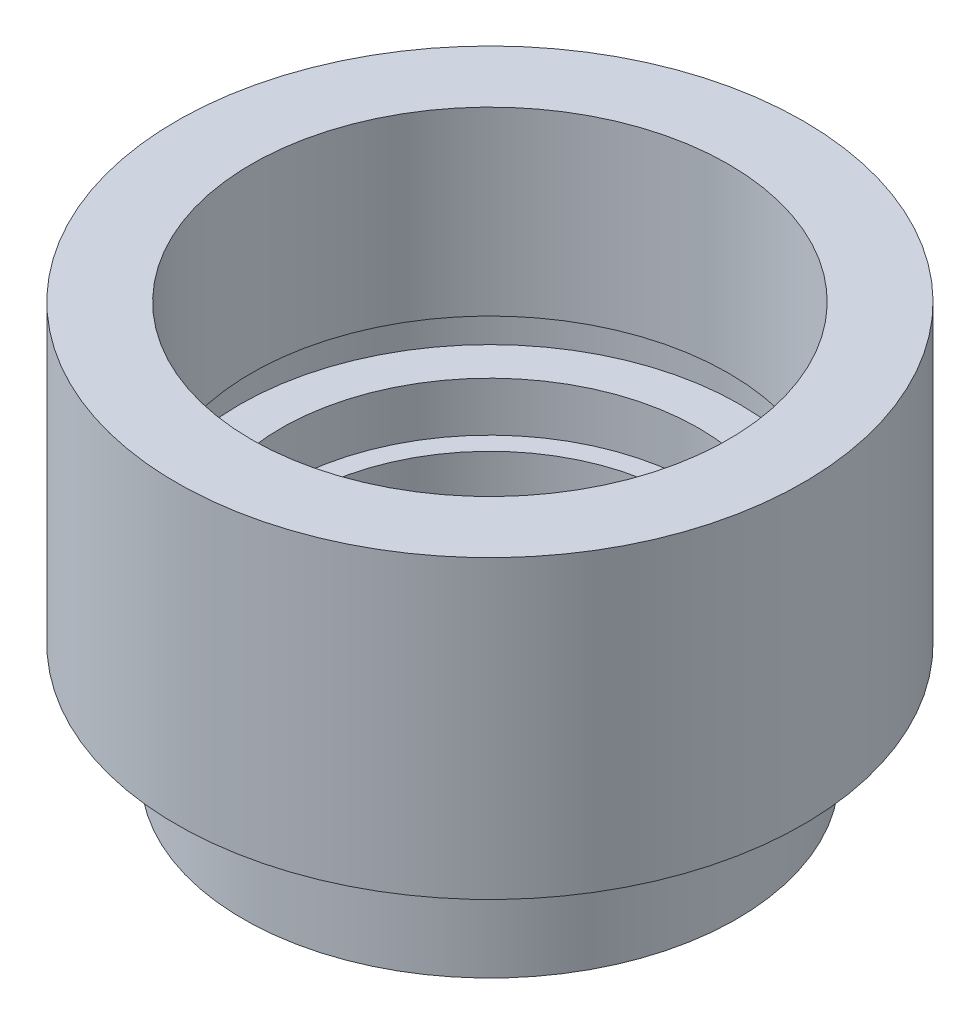
SolidWorks part; units mm, degrees
ref_plane "前视基准面" through (0, 0, 0) normal (0, 0, 1) x (1, 0, 0)
ref_plane "上视基准面" through (0, 0, 0) normal (0, 1, 0) x (1, 0, 0)
ref_plane "右视基准面" through (0, 0, 0) normal (1, 0, 0) x (0, 0, -1)
sketch "草图1" plane through (0, 0, 0) normal (0, 0, 1) x (1, 0, 0)
  line L0 (0, 0) -> (0, 21.8535) construction
  line L1 (5.75, 0) -> (7.5, 0)
  line L2 (7.5, 0) -> (7.5, 2.5)
  line L3 (7.5, 2.5) -> (7, 2.5)
  line L4 (7, 2.5) -> (7, 3.5)
  line L5 (7, 3.5) -> (9.525, 3.5)
  line L6 (9.525, 3.5) -> (9.525, 12.5)
  line L7 (9.525, 12.5) -> (7.25, 12.5)
  line L8 (7.25, 12.5) -> (7.25, 7)
  line L9 (7.25, 7) -> (7.6, 7)
  line L10 (7.6, 7) -> (7.6, 6)
  line L11 (7.6, 6) -> (6.35, 6)
  line L12 (6.35, 6) -> (6.35, 4.5)
  line L13 (6.35, 4.5) -> (5.75, 4.5)
  line L14 (5.75, 0) -> (5.75, 4.5)
  dimension "D1" = 12.5
  dimension "D2" = 9.525
  dimension "D3" = 7.25
  dimension "D4" = 6.35
  dimension "D5" = 1
  dimension "D6" = 1.5
  dimension "D7" = 5.75
  dimension "D8" = 7.5
  dimension "D9" = 1
  dimension "D10" = 3.5
  dimension "D11" = 4.5
  dimension "D12" = 7.6
  dimension "D13" = 7
revolve "旋转1" add sketch "草图1" angle 360 about L0
cosmetic thread "装饰螺纹线11"
cosmetic thread "装饰螺纹线12"
